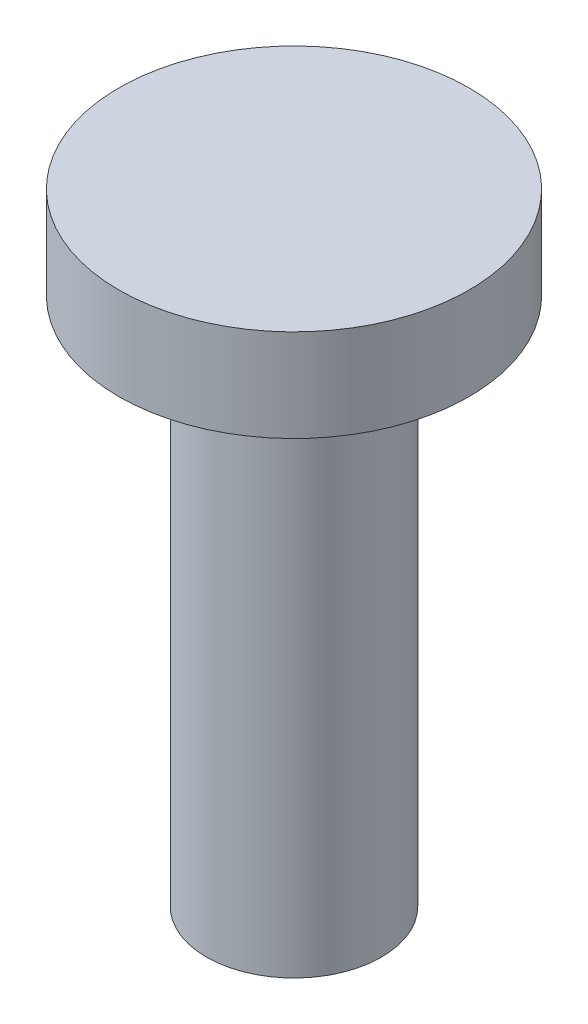
SolidWorks part; units mm, degrees
ref_plane "Front Plane" through (0, 0, 0) normal (0, 0, 1) x (1, 0, 0)
ref_plane "Top Plane" through (0, 0, 0) normal (0, 1, 0) x (1, 0, 0)
ref_plane "Right Plane" through (0, 0, 0) normal (1, 0, 0) x (0, 0, -1)
sketch "Sketch1" plane through (0, 0, 0) normal (0, 1, 0) x (1, 0, 0)
  circle A0 centre (0, 0) radius 3.175
  dimension "D1" = 6.35
extrude "Boss-Extrude1" add sketch "Sketch1" along normal blind 20
sketch "Sketch2" plane through (0, 0, 0) normal (0, -1, 0) x (1, 0, 0)
  circle A0 centre (0, 0) radius 1.675
  dimension "D1" = 3.35
extrude "Cut-Extrude1" cut sketch "Sketch2" against normal blind 12
sketch "Sketch4" plane through (0, 20, 0) normal (0, 1, 0) x (1, 0, 0)
  circle A0 centre (0, 0) radius 6.35
  dimension "D1" = 12.7
extrude "Boss-Extrude2" add sketch "Sketch4" along normal blind 2.54
sketch "Sketch6" plane through (0, 22.54, 0) normal (0, 1, 0) x (1, 0, 0)
  circle A0 centre (0, 0) radius 6.35
  dimension "D1" = 12.7
extrude "Boss-Extrude3" add sketch "Sketch6" against normal blind 3.35
